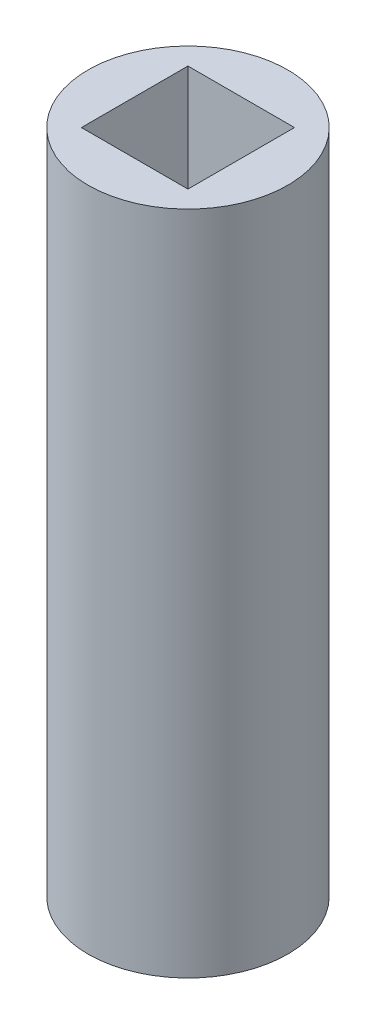
SolidWorks part; units mm, degrees
ref_plane "Plan de face" through (0, 0, 0) normal (0, 0, 1) x (1, 0, 0)
ref_plane "Plan de dessus" through (0, 0, 0) normal (0, 1, 0) x (1, 0, 0)
ref_plane "Plan de droite" through (0, 0, 0) normal (1, 0, 0) x (0, 0, -1)
sketch "Esquisse1" plane through (0, 0, 0) normal (0, 1, 0) x (1, 0, 0)
  line L1 (-1.6, -1.6) -> (1.6, -1.6)
  line L2 (-1.6, -1.6) -> (-1.6, 1.6)
  line L3 (-1.6, 1.6) -> (1.6, 1.6)
  line L4 (1.6, -1.6) -> (1.6, 1.6)
  line L5 (-1.6, -1.6) -> (1.6, 1.6) construction
  line L6 (-1.6, 1.6) -> (1.6, -1.6) construction
  circle A0 centre (0, 0) radius 3
  point P0 (0, 0)
  dimension "D2" = 6
  dimension "D1" = 3.2
extrude "Boss.-Extru.1" add sketch "Esquisse1" along normal blind 20
